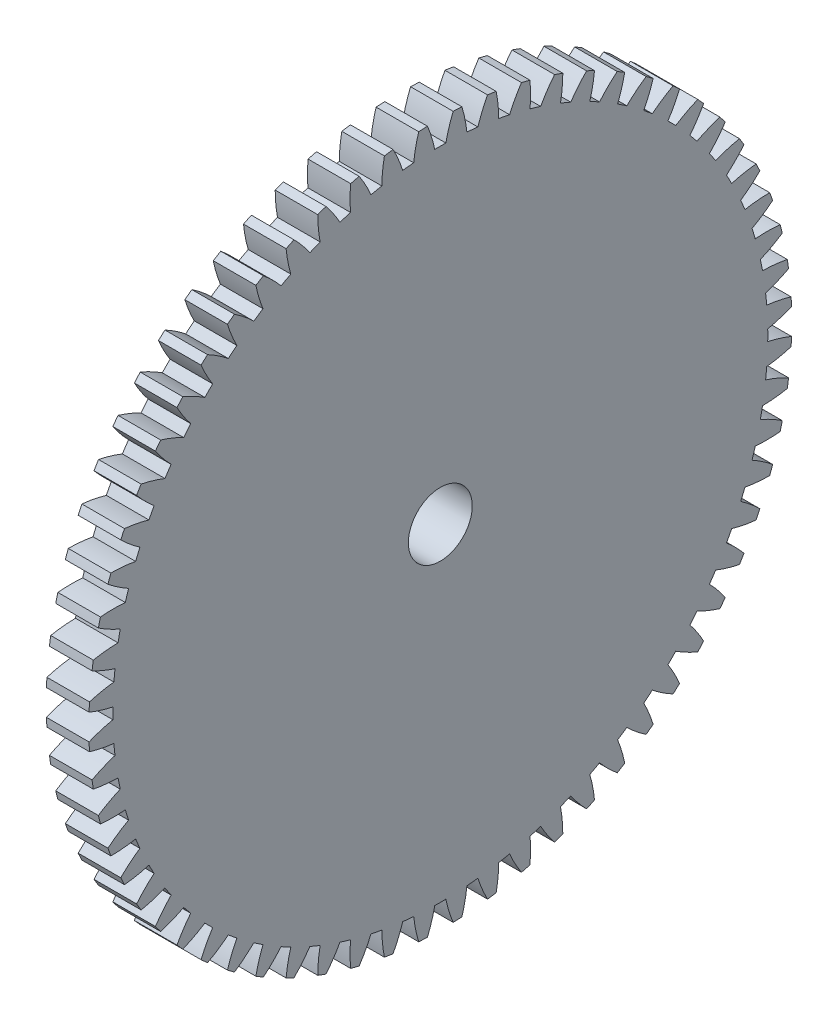
SolidWorks part; units mm, degrees
ref_plane "Plane1" through (0, 0, 0) normal (0, 0, 1) x (1, 0, 0)
ref_plane "Plane2" through (0, 0, 0) normal (0, 1, 0) x (1, 0, 0)
ref_plane "Plane3" through (0, 0, 0) normal (1, 0, 0) x (0, 0, -1)
other "Configuration Table"
sketch "HoldingSke" plane through (0, 0, 0) normal (0, 1, 0) x (1, 0, 0)
  line L0 (0, 0) -> (178.154, -365.2699)
  line L1 (-15, 0) -> (100, 0) construction
  line L2 (0, 0) -> (-2.1039, 2.3779)
  line L3 (0, 0) -> (-11.863, 4.5341)
  line L4 (0, 0) -> (3.7858, 7.762)
  line L5 (0, 0) -> (-11.8993, -4.4381)
  line L6 (0, 0) -> (-5.2639, -3.5516)
  line L7 (-2.1039, 2.3779) -> (0.6298, 14.7802)
  line L8 (-76.2, 54.61) -> (-65.4837, 54.61)
  line L9 (-67.7845, 28.3722) -> (-49.3413, 33.142)
  line L10 (-76.2, 71.12) -> (104.1128, 71.12)
  line L11 (0, 0) -> (-6.35, 0)
  line L12 (-76.2, 101.6) -> (-76.1428, 101.6)
  line L13 (24.9733, 27.94) -> (52.9518, 28.4284)
  line L14 (24.9733, 27.94) -> (24.9746, 27.94)
  line L15 (24.9733, 27.94) -> (100.4006, 29.5858)
  circle A0 centre (0, 0) radius 4.7625
  circle A1 centre (0, 0) radius 6.35
  circle A2 centre (0, 0) radius 6.35
  circle A3 centre (0, 0) radius 4.7625
  dimension "MHD" = 12.7
  dimension "Hub_dia" = 12.7
  dimension "Bore" = 9.525
  dimension "MBD" = 9.525
  dimension "Pitch" = 406.4
  dimension "Overall_len" = 12.7
  dimension "Thickness" = 6.35
  dimension "OAL" = 12.7001
  dimension "T_dim" = 10.7163
  dimension "Ap" = 14.5
  dimension "H" = 19.05
  dimension "Pitch_radius" = 180.3128
  dimension "Width" = 6.35
  dimension "Backlash" = 0.0571
  dimension "Addendum_fac" = 1
  dimension "Dedendum_fac" = 1.25
  dimension "Clearance_fac" = 0.25
  dimension "Dedendum_add" = 0.0013
sketch "BasProSke" plane through (0, 0, 0) normal (0, 1, 0) x (1, 0, 0)
  line L0 (-10, 0) -> (60, 0) construction
  line L1 (0, 0) -> (0, 52.3875)
  line L2 (0, 0) -> (6.35, 0)
  line L3 (6.35, 0) -> (6.35, 52.3875)
  line L4 (6.35, 52.3875) -> (0, 52.3875)
  dimension "Thickness" = 6.35
revolve "Base-Revolve" add sketch "BasProSke" angle 360 about L0
sketch "TooCutSke" plane through (0, 0, 0) normal (1, 0, 0) x (0, 0, -1)
  line L1 (0, 0) -> (0, 107) construction
  line L2 (0, 0) -> (-1.3467, 50.7821) construction
  line L3 (0, 0) -> (-4.984, 101.4518) construction
  line L4 (-1.3467, 50.7821) -> (-2.492, 50.7259) construction
  arc A0 (0.8249, 48.8074) -> (-0.8249, 48.8074) centre (0, 0) ccw
  arc A1 (1.9297, 52.3774) -> (-1.9297, 52.3774) centre (0, 0) ccw
  circle A2 centre (0, 0) radius 50.8 construction
  circle A3 centre (0, 0) radius 49.1819 construction
  arc A4 (-0.8249, 48.8074) -> (-1.9297, 52.3774) centre (-20.7068, 44.6104) ccw
  arc A5 (1.9297, 52.3774) -> (0.8249, 48.8074) centre (20.7068, 44.6104) ccw
  dimension "Half_CT" = 1.1467
extrude "ToothCut" cut sketch "TooCutSke" along normal through all
fillet "Breaks" [suppressed] radius 0.0318
fillet "RootFillets" [suppressed] radius 0.3981
pattern_circular "TeethCuts" count 64 every 5.625 about axis through (-10, 0, 0) along (1, 0, 0) of "ToothCut", "RootFillets", "Breaks"
sketch "HubNeaOneSke" plane through (0, 0, 0) normal (-1, 0, 0) x (0, 0, 1)
  circle A0 centre (0, 0) radius 6.35
  dimension "Diameter" = 12.7
extrude "HubNearOne" add sketch "HubNeaOneSke" along normal blind 6.3501
sketch "HubNeaBotSke" plane through (0, 0, 0) normal (-1, 0, 0) x (0, 0, 1)
  circle A0 centre (0, 0) radius 6.35
  dimension "Diameter" = 12.7
extrude "HubNearBoth" [suppressed] add sketch "HubNeaBotSke" along normal blind 3.175
ref_plane "FarPln" through (6.35, 0, 0) normal (1, 0, 0) x (0, 0, -1)
sketch "HubFarSke" plane through (6.35, 0, 0) normal (1, 0, 0) x (0, 0, -1)
  circle A0 centre (0, 0) radius 6.35
  dimension "Diameter" = 12.7
extrude "HubFar" [suppressed] add sketch "HubFarSke" along normal blind 3.175
sketch "BorSke" plane through (0, 0, 0) normal (1, 0, 0) x (0, 0, -1)
  circle A0 centre (0, 0) radius 4.7625
  dimension "Diameter" = 9.525
extrude "Bore" cut sketch "BorSke" along normal mid plane 25.4001
sketch "KeySke" plane through (0, 0, 0) normal (1, 0, 0) x (0, 0, -1)
  line L0 (-1.1913, 0) -> (-1.1913, 5.9538)
  line L1 (-1.1913, 5.9538) -> (1.1913, 5.9538)
  line L2 (1.1913, 5.9538) -> (1.1913, 0)
  line L3 (0, 0) -> (0, 34) construction
  line L4 (-1.1913, 0) -> (1.1913, 0)
  dimension "Offset" = 5.9538
  dimension "Width" = 2.3825
extrude "Keyway" [suppressed] cut sketch "KeySke" along normal mid plane 25.4001
pattern_circular "Keyway2" [suppressed] count 2 every 90 about axis through (-10, 0, 0) along (1, 0, 0)
equation "' \"Pitch@HoldingSke\" = 4"
equation "' \"Num_teeth@HoldingSke\" = 12"
equation "' \"Ap@HoldingSke\" =  20"
equation "' \"Ap@HoldingSke\" = 20"
equation "' \"Width@HoldingSke\" = 0.5"
equation "' \"Hub_dia@HoldingSke\"= 1"
equation "' \"Hub_dia@HoldingSke\" = 1"
equation "' \"Overall_len@HoldingSke\" = 1.0"
equation "' \"Bore@HoldingSke\" = 0.75"
equation "' \"T_dim@HoldingSke\" = 0.85"
equation "' \"Width@KeySke\" = 0.25"
equation "' \"Show_teeth@HoldingSke\" = 13"
equation "' \"Backlash@HoldingSke\" = 0.009"
equation "' \"Addendum_fac@HoldingSke\" = 1.0"
equation "' \"Dedendum_fac@HoldingSke\" = 1.25"
equation "' \"Dedendum_add@HoldingSke\" = 0.00005"
equation "' \"Clearance_fac@HoldingSke\" = 0.25"
equation "' \"Pitch@HoldingSke\" = 0.5"
equation "' \"Num_teeth@HoldingSke\" = 23"
equation "' \"Show_teeth@HoldingSke\" = 23"
equation "' \"Backlash@HoldingSke\" = 0.0375"
equation "\"Overcut_dia@TooCutSke\" = (\"Num_teeth@HoldingSke\" + 2 * \"Addendum_fac@HoldingSke\") / \"Pitch@HoldingSke\" + 0.002"
equation "\"Pitch_dia@TooCutSke\" = \"Num_teeth@HoldingSke\" / \"Pitch@HoldingSke\""
equation "\"Base_dia@TooCutSke\" = \"Num_teeth@HoldingSke\" / \"Pitch@HoldingSke\" * cos((\"Ap@HoldingSke\"  * 3.14159265 / 180))"
equation "\"Root_dia@TooCutSke\" = (\"Num_teeth@HoldingSke\" + 2) / \"Pitch@HoldingSke\" - 2 * (\"Addendum_fac@HoldingSke\" + \"Dedendum_fac@HoldingSke\") / \"Pitch@HoldingSke\" - \"Dedendum_add@HoldingSke\" * 2"
equation "\"Half_ang@TooCutSke\" = 180 / \"Num_teeth@HoldingSke\""
equation "\"Half_CT@TooCutSke\" = \"Num_teeth@HoldingSke\" / \"Pitch@HoldingSke\" * sin((3.14159265 / 2 / \"Num_teeth@HoldingSke\")) / 2 - 7 * \"Backlash@HoldingSke\" / 4"
equation "\"Flank_rad@TooCutSke\" = \"Num_teeth@HoldingSke\" / \"Pitch@HoldingSke\" / 5"
equation "\"Radius@RootFillets\" = \"Clearance_fac@HoldingSke\" / \"Pitch@HoldingSke\" + \"Dedendum_add@HoldingSke\""
equation "\"Break_rad@Breaks\" = 0.02 / \"Pitch@HoldingSke\""
equation "\"Thickness@HoldingSke\" = \"Width@HoldingSke\""
equation "\"OAL@HoldingSke\" = \"Thickness@HoldingSke\""
equation "\"MHD@HoldingSke\" = (\"Num_teeth@HoldingSke\" + 2) / \"Pitch@HoldingSke\" - 2 * (\"Addendum_fac@HoldingSke\" + \"Dedendum_fac@HoldingSke\")  / \"Pitch@HoldingSke\" - \"Dedendum_add@HoldingSke\" * 2"
equation "\"MBD@HoldingSke\" = (\"Num_teeth@HoldingSke\" + 2) / \"Pitch@HoldingSke\" - 2 * (\"Addendum_fac@HoldingSke\" + \"Dedendum_fac@HoldingSke\")  / \"Pitch@HoldingSke\" - \"Dedendum_add@HoldingSke\" * 2 - 0.002"
equation "\"MHD@HoldingSke\" = ((sgn( \"MHD@HoldingSke\" - \"Hub_dia@HoldingSke\" )-1)*( \"MHD@HoldingSke\" - \"Hub_dia@HoldingSke\" ))/-2+ \"Hub_dia@HoldingSke\""
equation "\"MBD@HoldingSke\" = ((sgn( \"MBD@HoldingSke\" - \"Bore@HoldingSke\" )-1)*( \"MBD@HoldingSke\" - \"Bore@HoldingSke\" ))/-2+ \"Bore@HoldingSke\""
equation "\"OAL@HoldingSke\" = ((sgn( \"OAL@HoldingSke\" - \"Overall_len@HoldingSke\" )+1)*( \"OAL@HoldingSke\" - \"Overall_len@HoldingSke\" ))/2 + \"Overall_len@HoldingSke\" + 0.000002"
equation "\"Num_teeth@TeethCuts\" = int( \"Show_teeth@HoldingSke\" ) + 1"
equation "\"Num_teeth@TeethCuts\" = ((sgn( \"Num_teeth@TeethCuts\" - \"Num_teeth@HoldingSke\" )-1)*( \"Num_teeth@TeethCuts\" - \"Num_teeth@HoldingSke\" ))/-2+ \"Num_teeth@HoldingSke\""
equation "\"Num_teeth@TeethCuts\" = ((sgn( \"Num_teeth@TeethCuts\" - 2.0)+1)*( \"Num_teeth@TeethCuts\" - 2.0))/2 +2.0"
equation "\"Angle@TeethCuts\" = 360.0 / \"Num_teeth@HoldingSke\""
equation "\"Diameter@BasProSke\" = (\"Num_teeth@HoldingSke\" + 2 * \"Addendum_fac@HoldingSke\") / \"Pitch@HoldingSke\""
equation "\"Thickness@BasProSke\"  = \"Thickness@HoldingSke\""
equation "' \"Fillet_rad@BasProSke\" =  \"Thickness@HoldingSke\" * 0.05"
equation "' \"Fillet_rad@BasProSke\" = \"Thickness@HoldingSke\" * 0.05"
equation "\"MHD@HoldingSke\" = ((sgn( \"MHD@HoldingSke\" - \"Root_dia@TooCutSke\" )-1)*( \"MHD@HoldingSke\" - \"Root_dia@TooCutSke\" ))/-2+ \"Root_dia@TooCutSke\""
equation "\"Diameter@HubNeaOneSke\" = \"MHD@HoldingSke\""
equation "\"Length@HubNearOne\" = \"OAL@HoldingSke\" - \"Thickness@BasProSke\""
equation "\"Diameter@HubNeaBotSke\" = \"MHD@HoldingSke\""
equation "\"Length@HubNearBoth\" = ( \"OAL@HoldingSke\" - \"Thickness@BasProSke\" ) / 2.0"
equation "\"Thickness@FarPln\" = \"Thickness@BasProSke\""
equation "\"Diameter@HubFarSke\" = \"MHD@HoldingSke\""
equation "\"Length@HubFar\" = ( \"OAL@HoldingSke\" - \"Thickness@BasProSke\" ) / 2.0"
equation "\"Diameter@BorSke\" = \"MBD@HoldingSke\""
equation "\"D1@Bore\" = \"OAL@HoldingSke\" * 2.0"
equation "\"D1@Keyway\" = \"OAL@HoldingSke\" * 2.0"
equation "\"Offset@KeySke\" = \"T_dim@HoldingSke\" - \"MBD@HoldingSke\" / 2.0"
